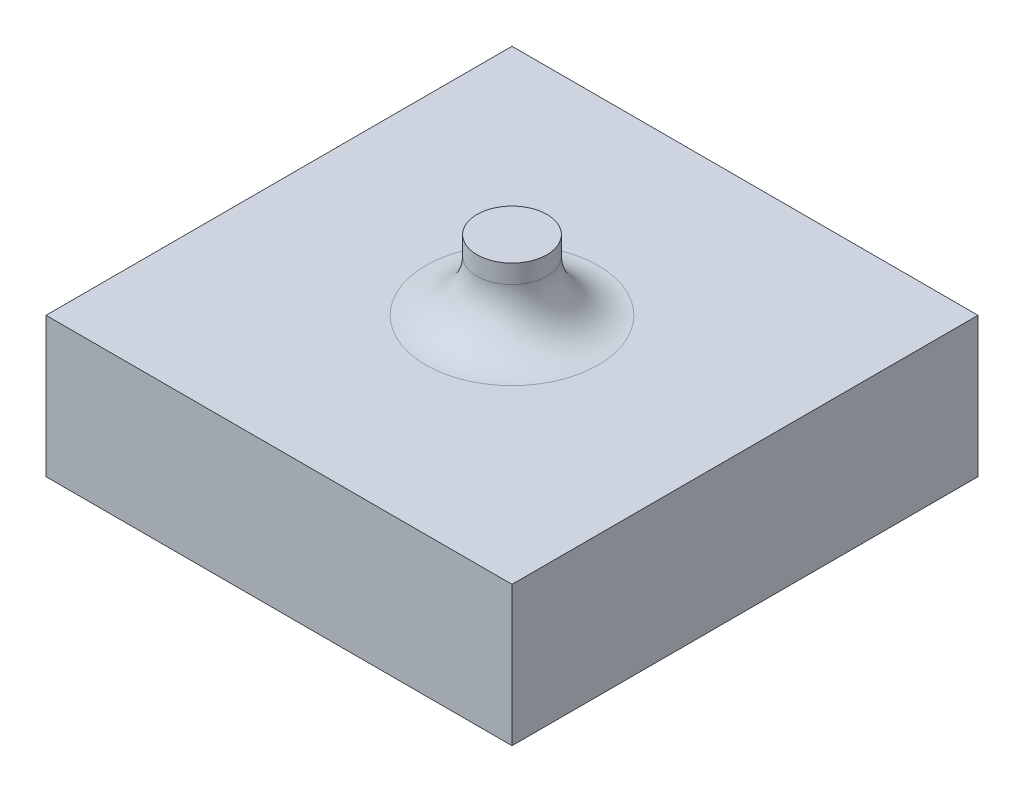
SolidWorks part; units mm, degrees
ref_plane "前视基准面" through (0, 0, 0) normal (0, 0, 1) x (1, 0, 0)
ref_plane "上视基准面" through (0, 0, 0) normal (0, 1, 0) x (1, 0, 0)
ref_plane "右视基准面" through (0, 0, 0) normal (1, 0, 0) x (0, 0, -1)
sketch "草图1" plane through (0, 0, 0) normal (0, 1, 0) x (1, 0, 0)
  line L1 (5, 5) -> (-5, 5)
  line L2 (5, 5) -> (5, -5)
  line L3 (5, -5) -> (-5, -5)
  line L4 (-5, 5) -> (-5, -5)
  line L5 (5, 5) -> (-5, -5) construction
  line L6 (5, -5) -> (-5, 5) construction
  point P0 (0, 0)
  dimension "D1" = 10
  dimension "D2" = 10
extrude "凸台-拉伸1" add sketch "草图1" along normal blind 3
sketch "草图2" plane through (0, 3, 0) normal (0, 1, 0) x (1, 0, 0)
  circle A0 centre (0, 0) radius 0.75
  dimension "D1" = 1.5
extrude "凸台-拉伸2" add sketch "草图2" along normal blind 1.5
fillet "圆角1" radius 1.1 1 edges at (0, 3, -0.75)
chamfer "倒角1" [suppressed] distance 0.1 angle 45
sketch "方向草图" plane through (0, 3, 0) normal (0, 1, 0) x (1, 0, 0)
  line L0 (-5, 5) -> (-5, -5) construction
  line L1 (-5, -5) -> (5, -5) construction
  line L2 (5, -5) -> (5, 5) construction
  line L3 (5, 5) -> (-5, 5) construction
  line L4 (-5, 5) -> (-5, -5) construction
  line L5 (-5, -5) -> (5, -5) construction
  line L6 (5, -5) -> (5, 5) construction
  line L7 (5, 5) -> (-5, 5) construction
  circle A0 centre (0, 0) radius 1.85 construction
  circle A1 centre (0, 0) radius 1.85
  point P7 (0, 0)
other "成形工具1"
